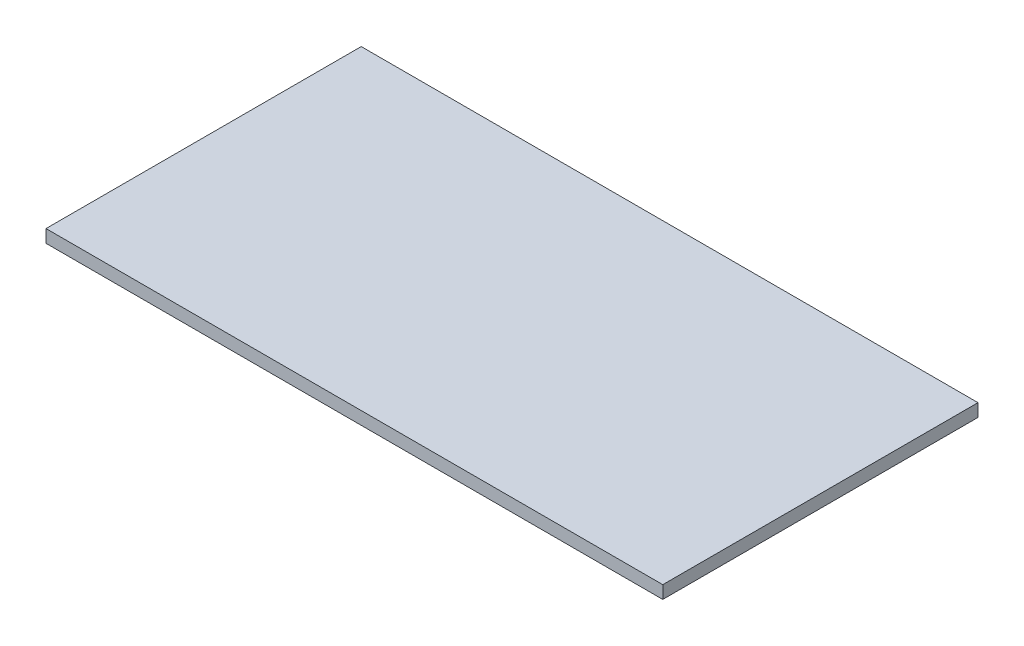
SolidWorks part; units mm, degrees
material "Cedar"
ref_plane "Front Plane" through (0, 0, 0) normal (0, 0, 1) x (1, 0, 0)
ref_plane "Top Plane" through (0, 0, 0) normal (0, 1, 0) x (1, 0, 0)
ref_plane "Right Plane" through (0, 0, 0) normal (1, 0, 0) x (0, 0, -1)
sketch "Sketch1" plane through (0, 0, 0) normal (0, 0, 1) x (1, 0, 0)
  line L1 (-286.5437, -5.9531) -> (286.5437, -5.9531)
  line L2 (-286.5437, -5.9531) -> (-286.5437, 5.9531)
  line L3 (-286.5437, 5.9531) -> (286.5437, 5.9531)
  line L4 (286.5437, -5.9531) -> (286.5437, 5.9531)
  line L5 (-286.5437, -5.9531) -> (286.5437, 5.9531) construction
  line L6 (-286.5437, 5.9531) -> (286.5437, -5.9531) construction
  point P0 (0, 0)
  dimension "D1" = 11.9062
  dimension "D2" = 573.0875
extrude "Boss-Extrude1" add sketch "Sketch1" against normal blind 292.8938
